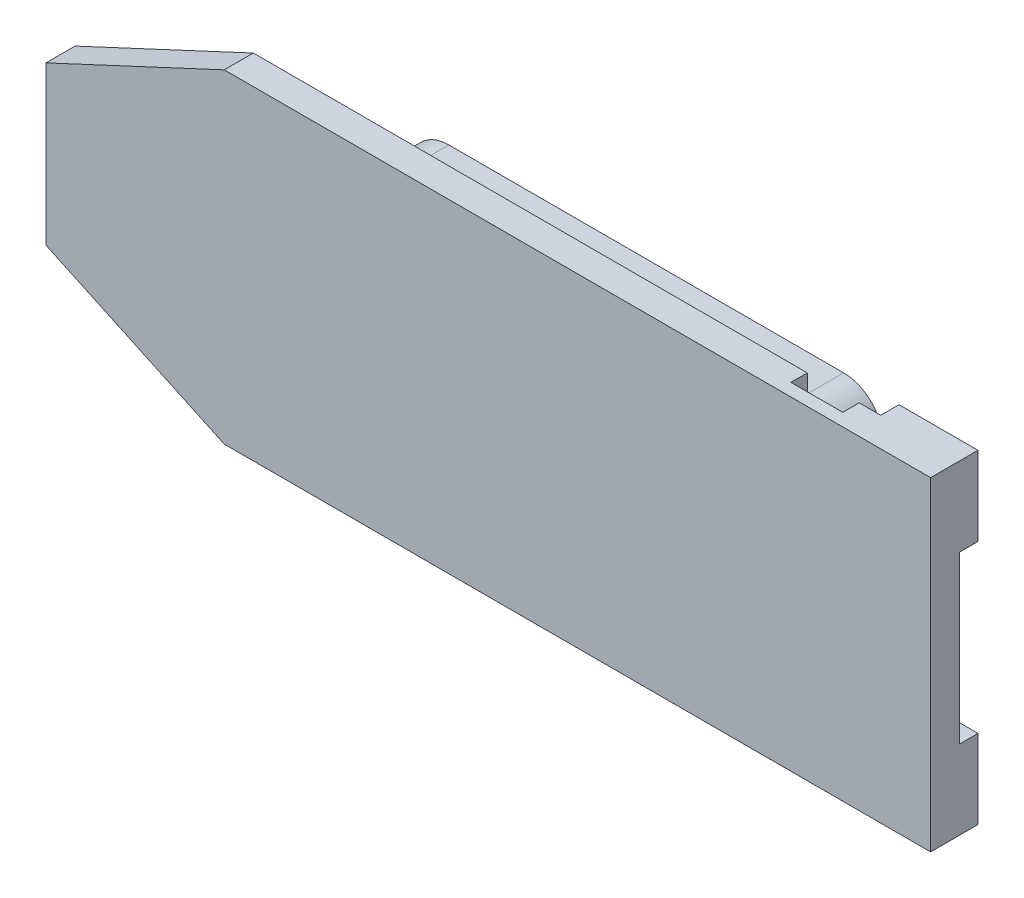
SolidWorks part; units mm, degrees
ref_plane "Front Plane" through (0, 0, 0) normal (0, 0, 1) x (1, 0, 0)
ref_plane "Top Plane" through (0, 0, 0) normal (0, 1, 0) x (1, 0, 0)
ref_plane "Right Plane" through (0, 0, 0) normal (1, 0, 0) x (0, 0, -1)
sketch "Sketch1" plane through (0, 0, 0) normal (0, 0, 1) x (1, 0, 0)
  line L0 (0, 69.7114) -> (0, -91.3316) construction
  line L1 (-87.5897, 0) -> (114.1992, 0) construction
  line L2 (-35.56, -6.35) -> (-35.56, 6.35)
  line L3 (-35.56, 6.35) -> (-21.23, 13.03)
  line L4 (-21.23, 13.03) -> (35.56, 13.03)
  line L5 (35.56, 13.03) -> (35.56, -13.03)
  line L6 (35.56, -13.03) -> (-21.23, -13.03)
  line L7 (-35.56, -6.35) -> (-21.23, -13.03)
  dimension "D1" = 12.7
  dimension "D2" = 26.06
  dimension "D3" = 56.79
  dimension "D4" = 71.12
extrude "Extrude1" add sketch "Sketch1" along normal blind 2.34
sketch "Sketch2" plane through (0, 0, 0) normal (0, 0, -1) x (-1, 0, 0)
  line L0 (-35.56, -13.03) -> (-35.56, 13.03) construction
  line L1 (-35.56, 13.03) -> (-29.21, 13.03)
  line L2 (-35.56, 13.03) -> (-35.56, 6.68)
  line L3 (-35.56, 6.68) -> (-29.21, 6.68)
  line L4 (-29.21, 13.03) -> (-29.21, 6.68)
  line L5 (-35.56, -6.68) -> (-29.21, -6.68)
  line L6 (-35.56, -6.68) -> (-35.56, -13.03)
  line L7 (-35.56, -13.03) -> (-29.21, -13.03)
  line L8 (-29.21, -6.68) -> (-29.21, -13.03)
  line L9 (21.23, -13.03) -> (-35.56, -13.03) construction
  line L10 (23.49, 3.175) -> (29.84, 3.175)
  line L11 (23.49, 3.175) -> (23.49, -3.175)
  line L12 (23.49, -3.175) -> (29.84, -3.175)
  line L13 (29.84, 3.175) -> (29.84, -3.175)
  line L14 (87.5897, 0) -> (-114.1992, 0) construction
  line L15 (-37.2377, 0) -> (37.6296, 0) construction
  line L16 (35.56, -6.35) -> (35.56, 6.35) construction
  line L17 (26.665, 13.9151) -> (26.665, -17.0509) construction
  line L18 (-32.385, 17.8349) -> (-32.385, -18.5404) construction
  line L19 (-38.3352, 9.855) -> (-23.6753, 9.855) construction
  line L20 (-24.9296, -9.855) -> (-37.2377, -9.855) construction
  line L21 (21.23, 13.03) -> (-35.56, 13.03) construction
  line L22 (-35.56, -13.03) -> (21.23, -13.03) construction
  circle A0 centre (-32.385, 9.855) radius 1.09
  circle A1 centre (-32.385, -9.855) radius 1.09
  circle A2 centre (26.665, 0) radius 1.09
  dimension "D3" = 2.18
  dimension "D4" = 2.18
  dimension "D5" = 3.175
  dimension "D1" = 6.35
  dimension "D2" = 5.72
extrude "Extrude2" add sketch "Sketch2" along normal blind 1.47
sketch "Sketch3" plane through (0, 0, 0) normal (0, 0, -1) x (-1, 0, 0)
  line L0 (-35.56, -13.03) -> (21.23, -13.03) construction
  line L1 (-27.48, -8.46) -> (-23.31, -8.46)
  line L2 (-27.48, -8.46) -> (-27.48, -13.03)
  line L3 (-27.48, -13.03) -> (-23.31, -13.03)
  line L4 (-23.31, -8.46) -> (-23.31, -13.03)
  line L5 (21.23, 13.03) -> (-35.56, 13.03) construction
  line L6 (-27.48, 13.03) -> (-23.31, 13.03)
  line L7 (-27.48, 13.03) -> (-27.48, 8.46)
  line L8 (-27.48, 8.46) -> (-23.31, 8.46)
  line L9 (-23.31, 13.03) -> (-23.31, 8.46)
  line L10 (35.56, -6.35) -> (35.56, 6.35) construction
  line L11 (30.99, 2.085) -> (35.56, 2.085)
  line L12 (30.99, 2.085) -> (30.99, -2.085)
  line L13 (30.99, -2.085) -> (35.56, -2.085)
  line L14 (35.56, 2.085) -> (35.56, -2.085)
  line L15 (-29.21, -13.03) -> (-29.21, -6.68) construction
  line L16 (-29.21, 6.68) -> (-29.21, 13.03) construction
  line L17 (87.5897, 0) -> (-114.1992, 0) construction
  line L18 (-39.759, 0) -> (38.6378, 0) construction
  point P20 (-29.21, 9.855)
  dimension "D1" = 4.57
  dimension "D2" = 4.17
  dimension "D3" = 1.73
  dimension "D4" = 1.73
  dimension "D5" = 4.57
  dimension "D6" = 4.17
  dimension "D7" = 4.17
  dimension "D8" = 4.57
extrude "Cut-Extrude1" cut sketch "Sketch3" against normal blind 1.32
fillet "Fillet1" radius 0.81 6 edges at (-30.99, -2.085, 0.66) (-30.99, 2.085, 0.66) (23.31, -8.46, 0.66) (27.48, -8.46, 0.66) (23.31, 8.46, 0.66) (27.48, 8.46, 0.66)
sketch "Sketch4" plane through (0, 0, 0) normal (0, 0, -1) x (-1, 0, 0)
  line L0 (-35.56, 13.03) -> (-35.56, -13.03) construction
  line L1 (-22.86, 7.94) -> (15.24, 7.94)
  line L2 (-22.86, 7.94) -> (-22.86, -7.94)
  line L3 (-22.86, -7.94) -> (15.24, -7.94)
  line L4 (15.24, 7.94) -> (15.24, -7.94)
  line L5 (87.5897, 0) -> (-114.1992, 0) construction
  line L6 (-42.0207, 0) -> (38.6136, 0) construction
  line L7 (-16.51, 16.5674) -> (-16.51, -16.0488) construction
  line L8 (8.89, 17.3678) -> (8.89, -18.45) construction
  circle A0 centre (-16.51, 0) radius 1.37
  circle A1 centre (8.89, 0) radius 1.37
  dimension "D6" = 2.74
  dimension "D7" = 2.74
  dimension "D8" = 6.35
  dimension "D9" = 6.35
  dimension "D1" = 12.7
  dimension "D2" = 38.1
  dimension "D3" = 15.88
  dimension "D4" = 6.35
  dimension "D5" = 31.75
extrude "Extrude3" add sketch "Sketch4" along normal blind 6.55
fillet "Fillet2" radius 3.18 4 edges at (-15.24, 7.94, -3.275) (22.86, 7.94, -3.275) (-15.24, -7.94, -3.275) (22.86, -7.94, -3.275)
